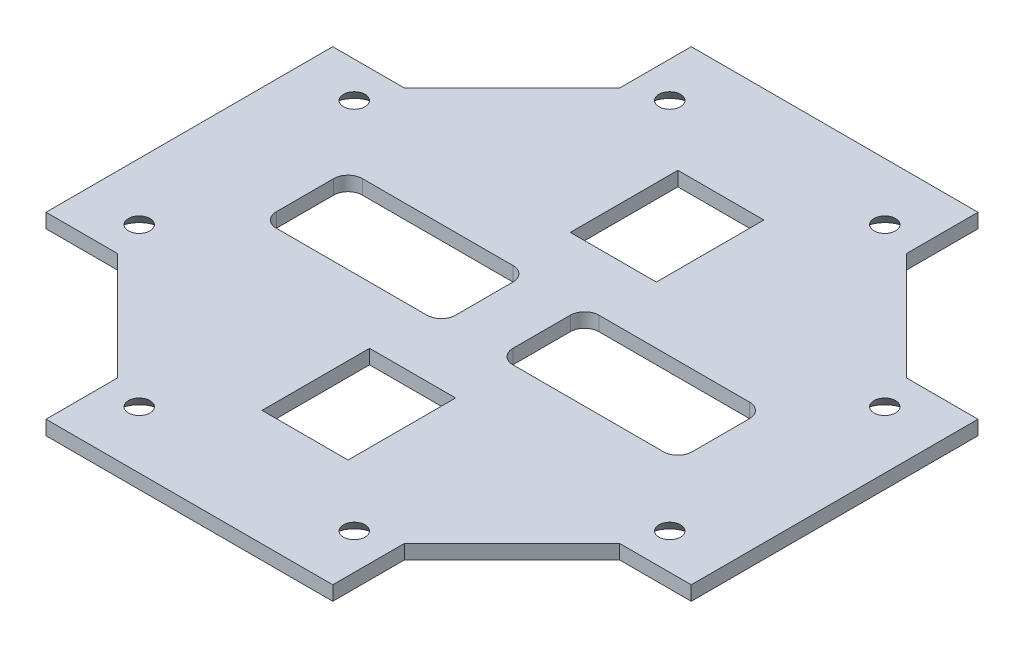
SolidWorks part; units mm, degrees
material "Plástico personalizado"
ref_plane "Plano frontal" through (0, 0, 0) normal (0, 0, 1) x (1, 0, 0)
ref_plane "Plano superior" through (0, 0, 0) normal (0, 1, 0) x (1, 0, 0)
ref_plane "Plano direito" through (0, 0, 0) normal (1, 0, 0) x (0, 0, -1)
sketch "Esboço1" plane through (0, 0, 0) normal (0, 1, 0) x (1, 0, 0)
  line L0 (-20, 35) -> (-20, 45)
  line L1 (-20, 35) -> (-35, 20)
  line L2 (-35, 20) -> (-45, 20)
  line L3 (-45, 20) -> (-45, -20)
  line L4 (-45, -20) -> (-35, -20)
  line L5 (-35, -20) -> (-20, -35)
  line L6 (-20, 45) -> (0, 45)
  line L7 (0, -45) -> (0, -28.8686)
  line L8 (0, 14.1314) -> (0, -13.8686)
  line L10 (-20, -35) -> (-20, -45)
  line L11 (-20, -45) -> (0, -45)
  line L12 (0, 29.1314) -> (0, 45)
  line L13 (-27, -5.8686) -> (-6, -5.8686)
  line L14 (-29, -3.8686) -> (-29, 4.1314)
  line L15 (-27, 6.1314) -> (-6, 6.1314)
  line L16 (-4, -3.8686) -> (-4, 4.1314)
  line L17 (-29, -5.8686) -> (-4, 6.1314) construction
  line L18 (-29, 6.1314) -> (-4, -5.8686) construction
  line L19 (0, 14.1314) -> (-6, 14.1314)
  line L20 (0, -13.8686) -> (-6, -13.8686)
  line L21 (0, 29.1314) -> (-6, 29.1314)
  line L22 (-6, 14.1314) -> (-6, 29.1314)
  line L24 (0, -28.8686) -> (-6, -28.8686)
  line L25 (-6, -13.8686) -> (-6, -28.8686)
  arc A0 (-27, 6.1314) -> (-29, 4.1314) centre (-27, 4.1314) ccw
  arc A1 (-29, -3.8686) -> (-27, -5.8686) centre (-27, -3.8686) ccw
  arc A2 (-6, -5.8686) -> (-4, -3.8686) centre (-6, -3.8686) ccw
  arc A3 (-4, 4.1314) -> (-6, 6.1314) centre (-6, 4.1314) ccw
  point P0 (-16.5, 0.1314)
  point P5 (-45, 0)
  point P31 (-10.3812, 20.6437)
  dimension "D11" = 2
  dimension "D2" = 10
  dimension "D3" = 16
  dimension "D4" = 10
  dimension "D5" = 10
  dimension "D6" = 40
  dimension "D7" = 25
  dimension "D8" = 25
  dimension "D9" = 12
  dimension "D10" = 25
  dimension "D12" = 15
  dimension "D13" = 45
  dimension "D14" = 8
  dimension "D15" = 20
  dimension "D16" = 20
  dimension "D17" = 15
  dimension "D19" = 8
extrude "Ressalto-extrusão1" add sketch "Esboço1" along normal blind 2
mirror "Espelhar1" about plane through (0, 0, 0) normal (1, 0, 0) of "Ressalto-extrusão1"
sketch "Esboço2" plane through (0, 2, 0) normal (0, 1, 0) x (1, 0, 0)
  line L0 (20, 45) -> (-20, 45) construction
  line L1 (-20, 45) -> (-20, 35) construction
  circle A0 centre (-15, 37) radius 1.5
  point P4 (-20, 40)
  dimension "D2" = 3
  dimension "D1" = 8
  dimension "D3" = 5
extrude "Corte-extrusão1" cut sketch "Esboço2" against normal through all draft 40 draft outward yes
mirror "Espelhar2" about plane through (0, 0, 0) normal (1, 0, 0) of "Corte-extrusão1"
mirror "Espelhar3" about plane through (0, 0, 0) normal (0, 0, 1) of "Espelhar2", "Corte-extrusão1"
pattern_circular "PadrãoCircular1" count 2 every 90 about axis through (0, 0, 0) along (0, 1, 0) of "Espelhar3", "Corte-extrusão1", "Espelhar2"
